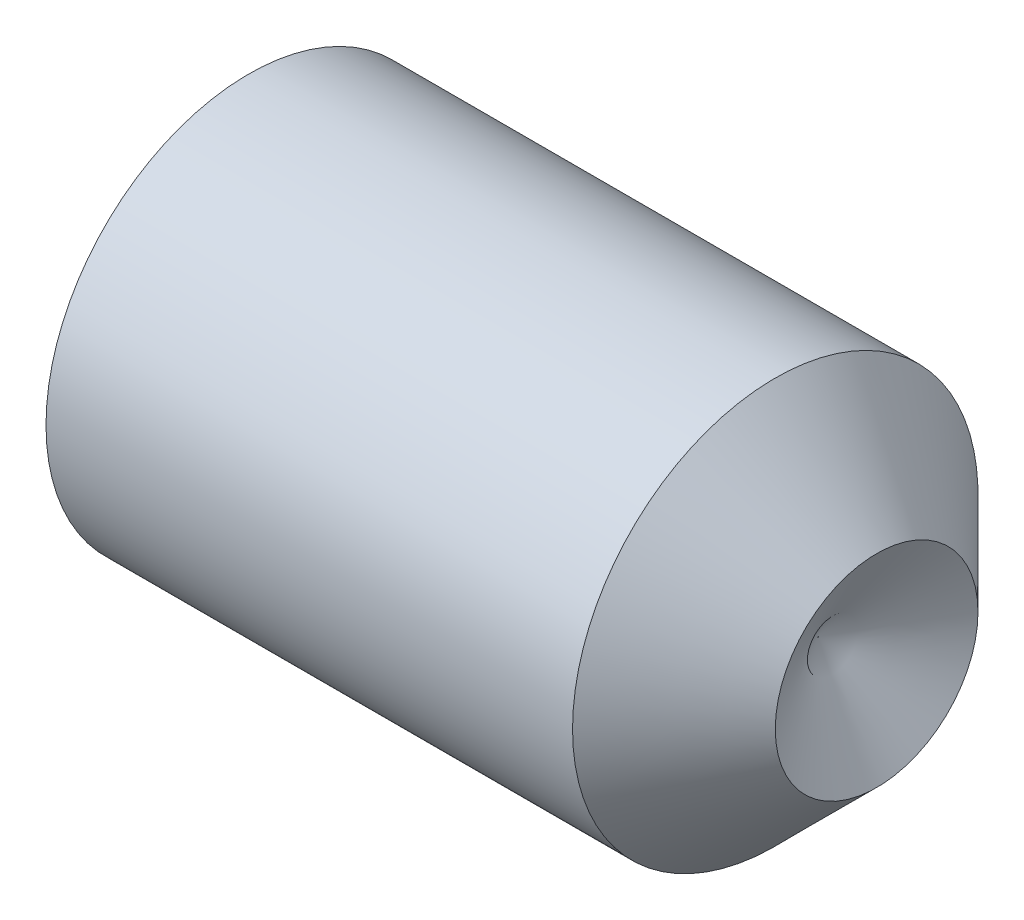
SolidWorks part; units mm, degrees
ref_plane "Plane1" through (0, 0, 0) normal (0, 0, 1) x (1, 0, 0)
ref_plane "Plane2" through (0, 0, 0) normal (0, 1, 0) x (1, 0, 0)
ref_plane "Plane3" through (0, 0, 0) normal (1, 0, 0) x (0, 0, -1)
sketch "BodySke" plane through (0, 0, 0) normal (0, 0, 1) x (1, 0, 0)
  line L0 (0, 0) -> (0, 2.055)
  line L1 (0, 2.055) -> (0.2569, 2.5)
  line L2 (0.2569, 2.5) -> (6.75, 2.5)
  line L3 (6.75, 2.5) -> (8, 1.25)
  line L4 (7.2783, 0) -> (0, 0)
  line L5 (-12.7, 0) -> (88.9, 0) construction
  line L6 (7.2783, 0) -> (8, 1.25)
  line L7 (8, 1.25) -> (8, 10.775) construction
  line L8 (0, -2.055) -> (0.2569, -2.5) construction
  line L9 (7.2783, 0) -> (8, -1.25) construction
  line L10 (6.75, -2.5) -> (8, -1.25) construction
  line L11 (0.4, 15.875) -> (0.4, -3.175) construction
  dimension "Length" = 8
  dimension "Diameter" = 5
  dimension "Drive_ch_ang" = 60
  dimension "Minor_dia" = 4.11
  dimension "Cup_nose_ang" = 45
  dimension "Cup_ang" = 120
  dimension "Cup_dia" = 2.5
  dimension "Advance" = 0.8
revolve "BaseBody" add sketch "BodySke" angle 360 about L5
cosmetic thread "ThreadCosmetic" [suppressed] parameters "Thread_minor"=4.11
sketch "Sketch2" plane through (0, 0, 0) normal (-1, 0, 0) x (0, 0, 1)
  line L0 (0.7217, 1.25) -> (-0.7217, 1.25)
  line L1 (-0.7217, 1.25) -> (-1.4434, 0)
  line L2 (0.7217, 1.25) -> (1.4434, 0)
  line L3 (0.7217, -1.25) -> (1.4434, 0)
  line L4 (0.7217, -1.25) -> (-0.7217, -1.25)
  line L5 (-0.7217, -1.25) -> (-1.4434, 0)
  dimension "Hex_size" = 2.5
  dimension "D2" = 1.25
  dimension "D3" = 1.25
extrude "Hex" cut sketch "Sketch2" against normal blind 3
sketch "ThdSchSke" plane through (0, 0, 0) normal (0, 0, 1) x (1, 0, 0)
  line L0 (0.2569, -2.055) -> (-0.0547, -2.5)
  line L1 (0.2569, -2.055) -> (0.5685, -2.5)
  line L2 (0.5685, -2.5) -> (0.5685, -3.125)
  line L3 (-3.175, 0) -> (5.1513, 0) construction
  line L4 (0.2569, 2.5) -> (0.2569, -2.5) construction
  line L5 (0.5685, -3.125) -> (-0.0547, -3.125)
  line L6 (-0.0547, -3.125) -> (-0.0547, -2.5)
  dimension "Thread_minor" = 4.11
  dimension "Diameter" = 5
  dimension "SideAngle" = 55
  dimension "VeeAngle" = 70
  dimension "Overcut" = 6.25
revolve "ThreadSchematic" [suppressed] cut sketch "ThdSchSke" angle 360 about L3
pattern_linear "ThdSchPat" [suppressed]
equation "\"D2@Sketch2\" = \"Hex_size@Sketch2\" / 2"
equation "\"D3@Sketch2\" = \"Hex_size@Sketch2\" / 2"
equation "\"Thread_minor@ThreadCosmetic\" = \"Minor_dia@BodySke\""
equation "\"Thread_minor@ThdSchSke\" = \"Thread_minor@ThreadCosmetic\""
equation "\"Diameter@ThdSchSke\" = \"Diameter@BodySke\""
equation "\"Overcut@ThdSchSke\" = \"Diameter@BodySke\" * 1.25"
equation "\"Num_threads@ThdSchPat\" = int( (\"Length@BodySke\" - ( ( ( \"Diameter@BodySke\" - \"Minor_dia@BodySke\" ) * 0.5 ) / tan( \"Drive_ch_ang@BodySke\" * 0.017453292 ) ) - ( ( ( \"Diameter@BodySke\" - \"Cup_dia@BodySke\" ) * 0.5 ) * tan( \"Cup_nose_ang@BodySke\" * 0.017453292 ) ) ) / \"Advance@BodySke\" + 0.999 )  + 1"
equation "\"Advance@ThdSchPat\" = (\"Length@BodySke\" - ( ( ( \"Diameter@BodySke\" - \"Minor_dia@BodySke\" ) * 0.5 ) / tan( \"Drive_ch_ang@BodySke\" * 0.017453292 ) ) - ( ( ( \"Diameter@BodySke\" - \"Cup_dia@BodySke\" ) * 0.5 ) * tan( \"Cup_nose_ang@BodySke\" * 0.017453292 ) ) ) /  (\"Num_threads@ThdSchPat\" - 1) 'relax it"
equation "' \"Num_threads@ThdSchPat\" = \"Num_threads@ThdSchPat\" - sgn( \"Num_threads@ThdSchPat\" - 1) '---chamfered tips only---"
